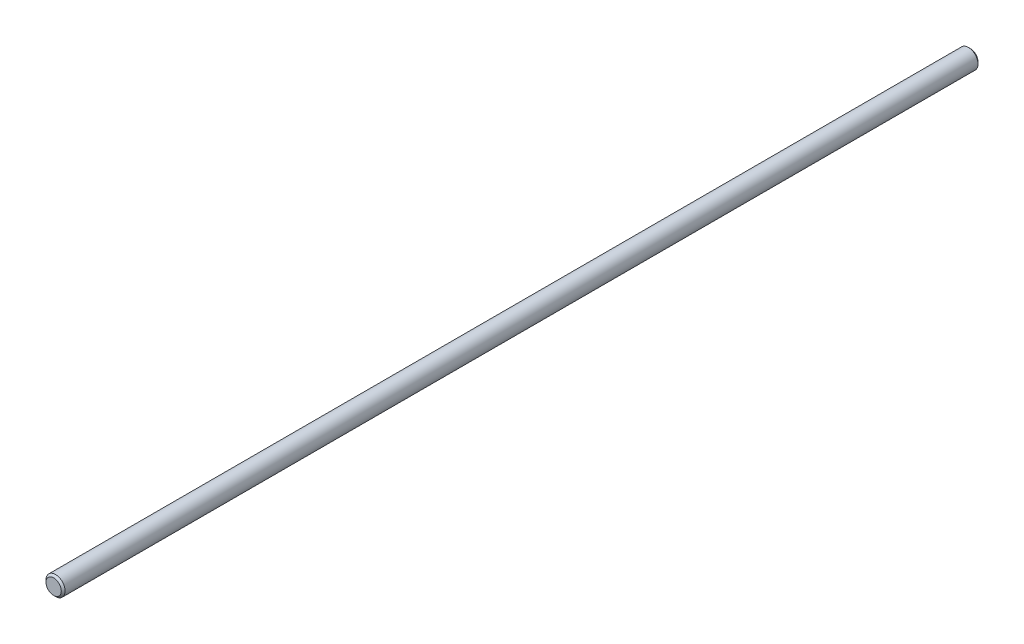
SolidWorks part; units mm, degrees
material "AISI 1045 Steel, cold drawn"
ref_plane "Front Plane" through (0, 0, 0) normal (0, 0, 1) x (1, 0, 0)
ref_plane "Top Plane" through (0, 0, 0) normal (0, 1, 0) x (1, 0, 0)
ref_plane "Right Plane" through (0, 0, 0) normal (1, 0, 0) x (0, 0, -1)
sketch "Sketch1" plane through (0, 0, 0) normal (0, 0, 1) x (1, 0, 0)
  line L0 (-12.7, 0) -> (12.7, 0) construction
  point P4 (0, 0)
  dimension "Diameter" = 25.4
sketch "Sketch2" plane through (0, 0, 0) normal (1, 0, 0) x (0, 0, -1)
  line L0 (609.6, 0) -> (-609.6, 0) construction
  point P4 (0, 0)
  dimension "Length" = 1219.2
sketch "Sketch3" plane through (0, 0, 0) normal (0, 0, 1) x (1, 0, 0)
  line L0 (-12.7, 0) -> (12.7, 0) construction
  circle A0 centre (0, 0) radius 12.7
  dimension "D1" = 25.4
extrude "Boss-Extrude1" add sketch "Sketch3" along normal mid plane 1219.2
chamfer "Chamfer1" distance 2.54 angle 45 2 edges at (12.7, 0, -609.6) (12.7, 0, 609.6)
sketch "Sketch4" plane through (0, 0, 0) normal (1, 0, 0) x (0, 0, -1)
  line L0 (607.06, 12.7) -> (-607.06, 12.7) construction
  line L2 (609.6, 12.7) -> (-609.6, 12.7) construction
  point P4 (609.6, 0)
  dimension "D2" = 1219.2
sketch "Sketch5" plane through (0, 0, 0) normal (1, 0, 0) x (0, 0, -1)
  line L0 (609.6, 0) -> (-609.6, 0) construction
  point P0 (-580.39, 0)
  point P1 (575.8712, 0)
  point P2 (-564.8113, 0)
  point P3 (580.39, 0)
  dimension "D1" = 29.21
  dimension "D2" = 29.21
  dimension "D3" = 44.7887
  dimension "D4" = 33.7288
equation "\"D1@Sketch3\"=\"Diameter@Sketch1\""
equation "\"D1@Boss-Extrude1\"=\"Length@Sketch2\""
equation "\"D1@Chamfer1\"=\"Diameter@Sketch1\"*.1"
equation "\"D2@Sketch4\"=\"Length@Sketch2\""
equation "\"D1@Sketch5\"=\"Diameter@Sketch1\"*1.15"
equation "\"D2@Sketch5\"=\"Diameter@Sketch1\"*1.15"
equation "\"D3@Sketch5\"=\"D1@Sketch5\" * 4 / 3 *1.15"
equation "\"D4@Sketch5\"=\"D1@Sketch5\" /  ( TAN ( 0.5236rad )  * 2 )  * 4 / 3"
